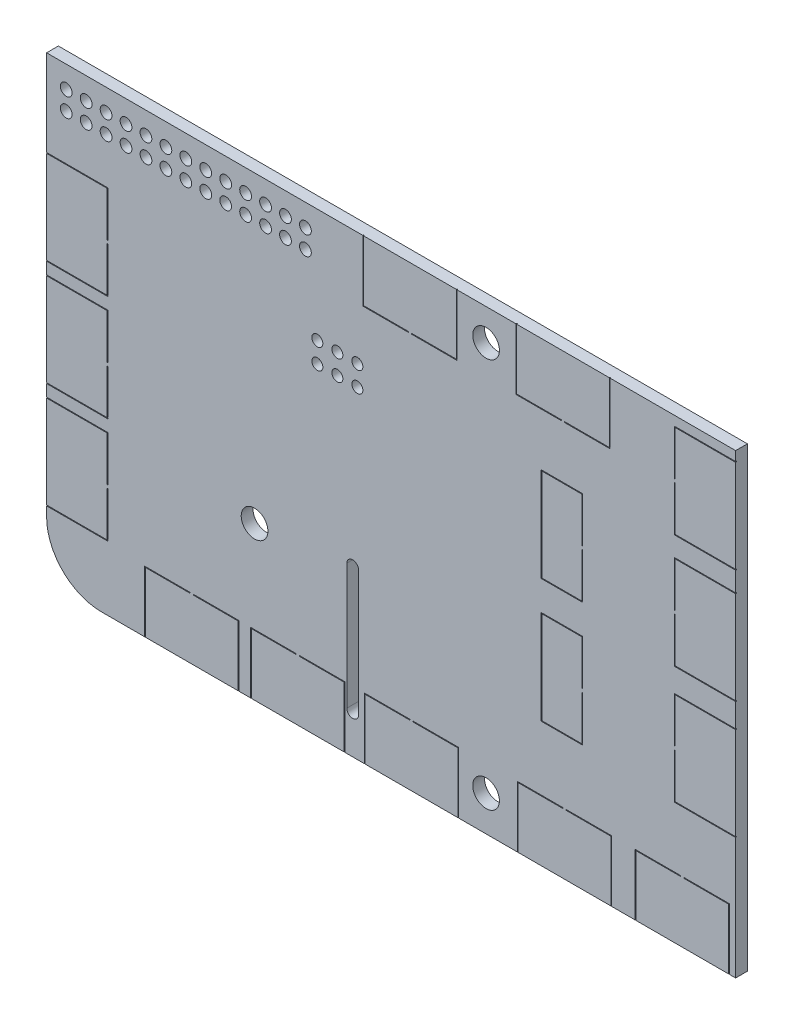
SolidWorks part; units mm, degrees
ref_plane "Plan de face" through (0, 0, 0) normal (0, 0, 1) x (1, 0, 0)
ref_plane "Plan de dessus" through (0, 0, 0) normal (0, 1, 0) x (1, 0, 0)
ref_plane "Plan de droite" through (0, 0, 0) normal (1, 0, 0) x (0, 0, -1)
sketch "Esquisse1" plane through (0, 0, 0) normal (0, 0, 1) x (1, 0, 0)
  line L0 (-4.9, -8.1) -> (-4.9, -24.1) construction
  line L1 (-36.9, -29.1) -> (43.9, -29.1)
  line L2 (-43.9, -22.1) -> (-43.9, 29.1)
  line L3 (-43.9, 29.1) -> (43.9, 29.1)
  line L4 (43.9, -29.1) -> (43.9, 29.1)
  line L5 (-43.9, -29.1) -> (43.9, 29.1) construction
  line L6 (-43.9, 29.1) -> (43.9, -29.1) construction
  line L7 (-4.15, -8.1) -> (-4.15, -24.1)
  line L8 (-5.65, -8.1) -> (-5.65, -24.1)
  circle A0 centre (12.1, 25.1) radius 1.7
  circle A1 centre (-17.4, -9.6) radius 1.7
  circle A2 centre (12.1, -24.6) radius 1.7
  arc A3 (-4.15, -8.1) -> (-5.65, -8.1) centre (-4.9, -8.1) ccw
  arc A4 (-5.65, -24.1) -> (-4.15, -24.1) centre (-4.9, -24.1) ccw
  arc A7 (-36.9, -29.1) -> (-43.9, -22.1) centre (-36.9, -22.1) cw
  point P0 (0, 0)
  point P14 (-4.9, -16.1)
  dimension "D3" = 56
  dimension "D7" = 3.4
  dimension "D8" = 3.4
  dimension "D11" = 3.4
  dimension "D20" = 7
  dimension "D1" = 87.8
  dimension "D2" = 58.2
  dimension "D4" = 4
  dimension "D5" = 26.5
  dimension "D6" = 19.5
  dimension "D9" = 56
  dimension "D10" = 4.5
  dimension "D12" = 21
  dimension "D13" = 5
  dimension "D14" = 1.5
  dimension "D15" = 39
extrude "Boss.-Extru.1" add sketch "Esquisse1" along normal blind 1.5
sketch "Esquisse2" plane through (0, 0, 0) normal (0, 0, 1) x (1, 0, 0)
  line L0 (-47.4847, 25.1) -> (2.4782, 25.1) construction
  line L1 (43.9, 29.1) -> (-43.9, 29.1) construction
  line L2 (-43.9, 29.1) -> (-43.9, -22.1) construction
  circle A0 centre (-41.4, 26.3) radius 0.75
  circle A1 centre (-41.4, 23.9) radius 0.75
  dimension "D1" = 4
  dimension "D3" = 1.5
  dimension "D2" = 2.5
  dimension "D4" = 2.8
extrude "Enlèv. mat.-Extru.3" cut sketch "Esquisse2" along normal through all
pattern_linear "Répétition linéaire1" count 13 spacing 2.54 along (1, 0, 0) of "Enlèv. mat.-Extru.3"
sketch "Esquisse3" plane through (0, 0, 1.5) normal (0, 0, 1) x (1, 0, 0)
  line L0 (43.9, 29.1) -> (-43.9, 29.1) construction
  line L1 (-13.7498, 13.3) -> (2.4782, 13.3) construction
  line L2 (-43.9, 29.1) -> (-43.9, -22.1) construction
  circle A0 centre (-9.4, 14.6) radius 0.7
  circle A1 centre (-9.4, 12) radius 0.7
  dimension "D1" = 14.5
  dimension "D3" = 1.4
  dimension "D2" = 15.8
  dimension "D4" = 34.5
extrude "Enlèv. mat.-Extru.4" cut sketch "Esquisse3" against normal blind 1.5
pattern_linear "Répétition linéaire2" count 3 spacing 2.55 along (1, 0, 0) of "Enlèv. mat.-Extru.4"
sketch "Esquisse5" plane through (0, 0, 1.5) normal (0, 0, 1) x (1, 0, 0)
  line L0 (-43.9, 29.1) -> (-43.9, -22.1) construction
  line L1 (-46, 18) -> (-36.2, 18)
  line L2 (-46, 18) -> (-46, 6.2)
  line L3 (-46, 6.2) -> (-36.2, 6.2)
  line L4 (-36.1, 18.1) -> (-36.1, 12.3)
  line L5 (-46, 18) -> (-36.2, 6.2) construction
  line L6 (-46, 6.2) -> (-36.2, 18) construction
  line L7 (-46.1, 18.1) -> (-36.1, 18.1)
  line L8 (-46.1, 18.1) -> (-46.1, 6.1)
  line L9 (-46.1, 6.1) -> (-36.1, 6.1)
  line L10 (-36.1, 12.3) -> (-36.2, 12.3)
  line L11 (-46.1, 18.1) -> (-36.1, 6.1) construction
  line L12 (-46.1, 6.1) -> (-36.1, 18.1) construction
  line L13 (43.9, 29.1) -> (-43.9, 29.1) construction
  line L14 (-36.2, 12.3) -> (-36.2, 18)
  line L15 (-36.1, 6.1) -> (-36.1, 11.9)
  line L16 (-36.1, 11.9) -> (-36.2, 11.9)
  line L17 (-36.2, 11.9) -> (-36.2, 6.2)
  line L18 (-46, 4.5) -> (-36.2, 4.5)
  line L19 (-46, 4.5) -> (-46, -7.3)
  line L20 (-46, -7.3) -> (-36.2, -7.3)
  line L21 (-36.1, 4.6) -> (-36.1, -1.2)
  line L22 (-46, 4.5) -> (-36.2, -7.3) construction
  line L23 (-46, -7.3) -> (-36.2, 4.5) construction
  line L24 (-46.1, 4.6) -> (-36.1, 4.6)
  line L25 (-46.1, 4.6) -> (-46.1, -7.4)
  line L26 (-46.1, -7.4) -> (-36.1, -7.4)
  line L27 (-36.1, -1.2) -> (-36.2, -1.2)
  line L28 (-46.1, 4.6) -> (-36.1, -7.4) construction
  line L29 (-46.1, -7.4) -> (-36.1, 4.6) construction
  line L30 (-36.2, -1.2) -> (-36.2, 4.5)
  line L31 (-36.1, -7.4) -> (-36.1, -1.6)
  line L32 (-36.1, -1.6) -> (-36.2, -1.6)
  line L33 (-36.2, -1.6) -> (-36.2, -7.3)
  line L34 (-46, -9) -> (-36.2, -9)
  line L35 (-46, -9) -> (-46, -20.8)
  line L36 (-46, -20.8) -> (-36.2, -20.8)
  line L37 (-36.1, -8.9) -> (-36.1, -14.7)
  line L38 (-46, -9) -> (-36.2, -20.8) construction
  line L39 (-46, -20.8) -> (-36.2, -9) construction
  line L40 (-46.1, -8.9) -> (-36.1, -8.9)
  line L41 (-46.1, -8.9) -> (-46.1, -20.9)
  line L42 (-46.1, -20.9) -> (-36.1, -20.9)
  line L43 (-36.1, -14.7) -> (-36.2, -14.7)
  line L44 (-46.1, -8.9) -> (-36.1, -20.9) construction
  line L45 (-46.1, -20.9) -> (-36.1, -8.9) construction
  line L46 (-36.2, -14.7) -> (-36.2, -9)
  line L47 (-36.1, -20.9) -> (-36.1, -15.1)
  line L48 (-36.1, -15.1) -> (-36.2, -15.1)
  line L49 (-36.2, -15.1) -> (-36.2, -20.8)
  line L50 (-3.4, -21.3) -> (2.4, -21.3)
  line L51 (-31.4, -21.3) -> (-25.6, -21.3)
  line L52 (-31.4, -21.3) -> (-31.4, -31.3)
  line L53 (-31.4, -31.3) -> (-19.4, -31.3)
  line L54 (-19.4, -21.3) -> (-19.4, -31.3)
  line L55 (-31.4, -21.3) -> (-19.4, -31.3) construction
  line L56 (-31.4, -31.3) -> (-19.4, -21.3) construction
  line L57 (-25.6, -21.3) -> (-25.6, -21.4)
  line L58 (-31.3, -21.4) -> (-31.3, -31.2)
  line L59 (-31.3, -31.2) -> (-19.5, -31.2)
  line L60 (-19.5, -21.4) -> (-19.5, -31.2)
  line L61 (-31.3, -21.4) -> (-19.5, -31.2) construction
  line L62 (-31.3, -31.2) -> (-19.5, -21.4) construction
  line L63 (-25.6, -21.4) -> (-31.3, -21.4)
  line L64 (-19.4, -21.3) -> (-25.2, -21.3)
  line L65 (-25.2, -21.3) -> (-25.2, -21.4)
  line L66 (-25.2, -21.4) -> (-19.5, -21.4)
  line L67 (-36.9, -29.1) -> (43.9, -29.1) construction
  line L68 (-17.9, -21.3) -> (-12.1, -21.3)
  line L69 (-17.9, -21.3) -> (-17.9, -31.3)
  line L70 (-17.9, -31.3) -> (-5.9, -31.3)
  line L71 (-5.9, -21.3) -> (-5.9, -31.3)
  line L72 (-17.9, -21.3) -> (-5.9, -31.3) construction
  line L73 (-17.9, -31.3) -> (-5.9, -21.3) construction
  line L74 (-12.1, -21.3) -> (-12.1, -21.4)
  line L75 (-17.8, -21.4) -> (-17.8, -31.2)
  line L76 (-17.8, -31.2) -> (-6, -31.2)
  line L77 (-6, -21.4) -> (-6, -31.2)
  line L78 (-17.8, -21.4) -> (-6, -31.2) construction
  line L79 (-17.8, -31.2) -> (-6, -21.4) construction
  line L80 (-12.1, -21.4) -> (-17.8, -21.4)
  line L81 (-5.9, -21.3) -> (-11.7, -21.3)
  line L82 (-11.7, -21.3) -> (-11.7, -21.4)
  line L83 (-11.7, -21.4) -> (-6, -21.4)
  line L84 (-3.4, -21.3) -> (-3.4, -31.3)
  line L85 (-3.4, -31.3) -> (8.6, -31.3)
  line L86 (8.6, -21.3) -> (8.6, -31.3)
  line L87 (-3.4, -21.3) -> (8.6, -31.3) construction
  line L88 (-3.4, -31.3) -> (8.6, -21.3) construction
  line L89 (2.4, -21.3) -> (2.4, -21.4)
  line L90 (-3.3, -21.4) -> (-3.3, -31.2)
  line L91 (-3.3, -31.2) -> (8.5, -31.2)
  line L92 (8.5, -21.4) -> (8.5, -31.2)
  line L93 (-3.3, -21.4) -> (8.5, -31.2) construction
  line L94 (-3.3, -31.2) -> (8.5, -21.4) construction
  line L95 (2.4, -21.4) -> (-3.3, -21.4)
  line L96 (8.6, -21.3) -> (2.8, -21.3)
  line L97 (2.8, -21.3) -> (2.8, -21.4)
  line L98 (2.8, -21.4) -> (8.5, -21.4)
  line L99 (16.1, -21.3) -> (21.9, -21.3)
  line L100 (16.1, -21.3) -> (16.1, -31.3)
  line L101 (16.1, -31.3) -> (28.1, -31.3)
  line L102 (28.1, -21.3) -> (28.1, -31.3)
  line L103 (16.1, -21.3) -> (28.1, -31.3) construction
  line L104 (16.1, -31.3) -> (28.1, -21.3) construction
  line L105 (21.9, -21.3) -> (21.9, -21.4)
  line L106 (16.2, -21.4) -> (16.2, -31.2)
  line L107 (16.2, -31.2) -> (28, -31.2)
  line L108 (28, -21.4) -> (28, -31.2)
  line L109 (16.2, -21.4) -> (28, -31.2) construction
  line L110 (16.2, -31.2) -> (28, -21.4) construction
  line L111 (21.9, -21.4) -> (16.2, -21.4)
  line L112 (28.1, -21.3) -> (22.3, -21.3)
  line L113 (22.3, -21.3) -> (22.3, -21.4)
  line L114 (22.3, -21.4) -> (28, -21.4)
  line L115 (31.1, -21.3) -> (36.9, -21.3)
  line L116 (31.1, -21.3) -> (31.1, -31.3)
  line L117 (31.1, -31.3) -> (43.1, -31.3)
  line L118 (43.1, -21.3) -> (43.1, -31.3)
  line L119 (31.1, -21.3) -> (43.1, -31.3) construction
  line L120 (31.1, -31.3) -> (43.1, -21.3) construction
  line L121 (36.9, -21.3) -> (36.9, -21.4)
  line L122 (31.2, -21.4) -> (31.2, -31.2)
  line L123 (31.2, -31.2) -> (43, -31.2)
  line L124 (43, -21.4) -> (43, -31.2)
  line L125 (31.2, -21.4) -> (43, -31.2) construction
  line L126 (31.2, -31.2) -> (43, -21.4) construction
  line L127 (36.9, -21.4) -> (31.2, -21.4)
  line L128 (43.1, -21.3) -> (37.3, -21.3)
  line L129 (37.3, -21.3) -> (37.3, -21.4)
  line L130 (37.3, -21.4) -> (43, -21.4)
  line L131 (36.1, -7.4) -> (36.2, -7.4)
  line L132 (36.1, -1.6) -> (46.1, -1.6)
  line L133 (36.1, -1.6) -> (36.1, -7.4)
  line L134 (36.1, -13.6) -> (46.1, -13.6)
  line L135 (46.1, -1.6) -> (46.1, -13.6)
  line L136 (36.1, -1.6) -> (46.1, -13.6) construction
  line L137 (36.1, -13.6) -> (46.1, -1.6) construction
  line L138 (36.2, -7.4) -> (36.2, -1.7)
  line L139 (36.2, -13.5) -> (46, -13.5)
  line L140 (36.1, -13.6) -> (36.1, -7.8)
  line L141 (36.2, -1.7) -> (46, -1.7)
  line L142 (46, -13.5) -> (46, -1.7)
  line L143 (36.2, -13.5) -> (46, -1.7) construction
  line L144 (36.2, -1.7) -> (46, -13.5) construction
  line L145 (36.1, -7.8) -> (36.2, -7.8)
  line L146 (36.2, -7.8) -> (36.2, -13.5)
  line L147 (43.9, -29.1) -> (43.9, 29.1) construction
  line L148 (36.1, 7.6) -> (36.2, 7.6)
  line L149 (36.1, 13.4) -> (46.1, 13.4)
  line L150 (36.1, 13.4) -> (36.1, 7.6)
  line L151 (36.1, 1.4) -> (46.1, 1.4)
  line L152 (46.1, 13.4) -> (46.1, 1.4)
  line L153 (36.1, 13.4) -> (46.1, 1.4) construction
  line L154 (36.1, 1.4) -> (46.1, 13.4) construction
  line L155 (36.2, 7.6) -> (36.2, 13.3)
  line L156 (36.2, 1.5) -> (46, 1.5)
  line L157 (36.1, 1.4) -> (36.1, 7.2)
  line L158 (36.2, 13.3) -> (46, 13.3)
  line L159 (46, 1.5) -> (46, 13.3)
  line L160 (36.2, 1.5) -> (46, 13.3) construction
  line L161 (36.2, 13.3) -> (46, 1.5) construction
  line L162 (36.1, 7.2) -> (36.2, 7.2)
  line L163 (36.2, 7.2) -> (36.2, 1.5)
  line L164 (36.1, 22.1) -> (36.2, 22.1)
  line L165 (36.1, 27.9) -> (46.1, 27.9)
  line L166 (36.1, 27.9) -> (36.1, 22.1)
  line L167 (36.1, 15.9) -> (46.1, 15.9)
  line L168 (46.1, 27.9) -> (46.1, 15.9)
  line L169 (36.1, 27.9) -> (46.1, 15.9) construction
  line L170 (36.1, 15.9) -> (46.1, 27.9) construction
  line L171 (36.2, 22.1) -> (36.2, 27.8)
  line L172 (36.2, 16) -> (46, 16)
  line L173 (36.1, 15.9) -> (36.1, 21.7)
  line L174 (36.2, 27.8) -> (46, 27.8)
  line L175 (46, 16) -> (46, 27.8)
  line L176 (36.2, 16) -> (46, 27.8) construction
  line L177 (36.2, 27.8) -> (46, 16) construction
  line L178 (36.1, 21.7) -> (36.2, 21.7)
  line L179 (36.2, 21.7) -> (36.2, 16)
  line L180 (15.9, 21.3) -> (21.7, 21.3)
  line L181 (15.9, 31.3) -> (27.9, 31.3)
  line L182 (15.9, 31.3) -> (15.9, 21.3)
  line L183 (21.7, 21.3) -> (21.7, 21.4)
  line L184 (27.9, 31.3) -> (27.9, 21.3)
  line L185 (15.9, 31.3) -> (27.9, 21.3) construction
  line L186 (15.9, 21.3) -> (27.9, 31.3) construction
  line L187 (21.7, 21.4) -> (16, 21.4)
  line L188 (16, 21.4) -> (16, 31.2)
  line L189 (16, 31.2) -> (27.8, 31.2)
  line L190 (27.8, 21.4) -> (27.8, 31.2)
  line L191 (16, 21.4) -> (27.8, 31.2) construction
  line L192 (16, 31.2) -> (27.8, 21.4) construction
  line L193 (27.9, 21.3) -> (22.1, 21.3)
  line L194 (22.1, 21.3) -> (22.1, 21.4)
  line L195 (22.1, 21.4) -> (27.8, 21.4)
  line L196 (-3.6, 21.3) -> (2.2, 21.3)
  line L197 (-3.6, 31.3) -> (8.4, 31.3)
  line L198 (-3.6, 31.3) -> (-3.6, 21.3)
  line L199 (2.2, 21.3) -> (2.2, 21.4)
  line L200 (8.4, 31.3) -> (8.4, 21.3)
  line L201 (-3.6, 31.3) -> (8.4, 21.3) construction
  line L202 (-3.6, 21.3) -> (8.4, 31.3) construction
  line L203 (2.2, 21.4) -> (-3.5, 21.4)
  line L204 (-3.5, 21.4) -> (-3.5, 31.2)
  line L205 (-3.5, 31.2) -> (8.3, 31.2)
  line L206 (8.3, 21.4) -> (8.3, 31.2)
  line L207 (-3.5, 21.4) -> (8.3, 31.2) construction
  line L208 (-3.5, 31.2) -> (8.3, 21.4) construction
  line L209 (8.4, 21.3) -> (2.6, 21.3)
  line L210 (2.6, 21.3) -> (2.6, 21.4)
  line L211 (2.6, 21.4) -> (8.3, 21.4)
  line L212 (24.4, 14.6) -> (24.4, 8.8)
  line L213 (19.1, 14.6) -> (24.4, 14.6)
  line L214 (19.1, 14.6) -> (19.1, 2.6)
  line L215 (19.1, 2.6) -> (24.4, 2.6)
  line L216 (24.4, 8.8) -> (24.3, 8.8)
  line L217 (19.1, 14.6) -> (24.4, 2.6) construction
  line L218 (19.1, 2.6) -> (24.4, 14.6) construction
  line L219 (19.2, 2.7) -> (24.3, 2.7)
  line L220 (19.2, 2.7) -> (19.2, 14.5)
  line L221 (19.2, 14.5) -> (24.3, 14.5)
  line L222 (24.3, 8.8) -> (24.3, 14.5)
  line L223 (19.2, 2.7) -> (24.3, 14.5) construction
  line L224 (19.2, 14.5) -> (24.3, 2.7) construction
  line L225 (24.4, 2.6) -> (24.4, 8.4)
  line L226 (24.4, 8.4) -> (24.3, 8.4)
  line L227 (24.3, 8.4) -> (24.3, 2.7)
  line L228 (24.4, -1.15) -> (24.4, -6.95)
  line L229 (19.1, -1.15) -> (24.4, -1.15)
  line L230 (19.1, -1.15) -> (19.1, -13.15)
  line L231 (19.1, -13.15) -> (24.4, -13.15)
  line L232 (24.4, -6.95) -> (24.3, -6.95)
  line L233 (19.1, -1.15) -> (24.4, -13.15) construction
  line L234 (19.1, -13.15) -> (24.4, -1.15) construction
  line L235 (19.2, -13.05) -> (24.3, -13.05)
  line L236 (19.2, -13.05) -> (19.2, -1.25)
  line L237 (19.2, -1.25) -> (24.3, -1.25)
  line L238 (24.3, -6.95) -> (24.3, -1.25)
  line L239 (19.2, -13.05) -> (24.3, -1.25) construction
  line L240 (19.2, -1.25) -> (24.3, -13.05) construction
  line L241 (24.4, -13.15) -> (24.4, -7.35)
  line L242 (24.4, -7.35) -> (24.3, -7.35)
  line L243 (24.3, -7.35) -> (24.3, -13.05)
  point P0 (-41.1, 12.1)
  point P5 (-41.1, 12.1)
  point P18 (-41.1, -1.4)
  point P23 (-41.1, -1.4)
  point P32 (-41.1, -14.9)
  point P37 (-41.1, -14.9)
  point P46 (-25.4, -26.3)
  point P51 (-25.4, -26.3)
  point P62 (-11.9, -26.3)
  point P67 (-11.9, -26.3)
  point P76 (2.6, -26.3)
  point P81 (2.6, -26.3)
  point P90 (22.1, -26.3)
  point P95 (22.1, -26.3)
  point P104 (37.1, -26.3)
  point P109 (37.1, -26.3)
  point P118 (41.1, -7.6)
  point P125 (41.1, -7.6)
  point P134 (41.1, 7.4)
  point P140 (41.1, 7.4)
  point P148 (41.1, 21.9)
  point P154 (41.1, 21.9)
  point P162 (21.9, 26.3)
  point P167 (21.9, 26.3)
  point P172 (2.4, 26.3)
  point P181 (2.4, 26.3)
  point P190 (21.75, 8.6)
  point P195 (21.75, 8.6)
  point P200 (21.75, -7.15)
  point P209 (21.75, -7.15)
  dimension "D1" = 5.8
  dimension "D2" = 12
  dimension "D3" = 0.1
  dimension "D4" = 5.8
  dimension "D5" = 11
  dimension "D6" = 10
  dimension "D7" = 0.1
  dimension "D8" = 0.1
  dimension "D9" = 7.8
  dimension "D10" = 12
  dimension "D11" = 0.1
  dimension "D12" = 5.8
  dimension "D13" = 5.8
  dimension "D14" = 10
  dimension "D15" = 0.1
  dimension "D16" = 0.1
  dimension "D17" = 1.5
  dimension "D18" = 7.8
  dimension "D19" = 12
  dimension "D20" = 5.8
  dimension "D21" = 5.8
  dimension "D22" = 10
  dimension "D23" = 0.1
  dimension "D24" = 0.1
  dimension "D25" = 1.5
  dimension "D26" = 7.8
  dimension "D27" = 0.1
  dimension "D28" = 12
  dimension "D29" = 0.1
  dimension "D30" = 0.1
  dimension "D31" = 12.5
  dimension "D32" = 5.8
  dimension "D33" = 5.8
  dimension "D34" = 7.8
  dimension "D35" = 0.1
  dimension "D36" = 10
  dimension "D37" = 0.1
  dimension "D38" = 5.8
  dimension "D39" = 5.8
  dimension "D40" = 0.1
  dimension "D41" = 10
  dimension "D42" = 1.5
  dimension "D43" = 7.8
  dimension "D44" = 0.1
  dimension "D45" = 12
  dimension "D46" = 0.1
  dimension "D47" = 5.8
  dimension "D48" = 5.8
  dimension "D49" = 0.1
  dimension "D50" = 10
  dimension "D51" = 0.1
  dimension "D52" = 12
  dimension "D53" = 2.5
  dimension "D54" = 7.8
  dimension "D55" = 0.1
  dimension "D56" = 5.8
  dimension "D57" = 5.8
  dimension "D58" = 0.1
  dimension "D59" = 10
  dimension "D60" = 0.1
  dimension "D61" = 12
  dimension "D62" = 7.8
  dimension "D63" = 7.5
  dimension "D64" = 0.1
  dimension "D65" = 5.8
  dimension "D66" = 5.8
  dimension "D67" = 0.1
  dimension "D68" = 10
  dimension "D69" = 0.1
  dimension "D70" = 12
  dimension "D71" = 7.8
  dimension "D72" = 3
  dimension "D73" = 12
  dimension "D74" = 7.8
  dimension "D75" = 10
  dimension "D76" = 15.5
  dimension "D77" = 0.1
  dimension "D78" = 0.1
  dimension "D79" = 5.8
  dimension "D80" = 0.1
  dimension "D81" = 5.8
  dimension "D82" = 12
  dimension "D83" = 0.1
  dimension "D84" = 0.1
  dimension "D85" = 10
  dimension "D86" = 5.8
  dimension "D87" = 0.1
  dimension "D88" = 5.8
  dimension "D89" = 7.8
  dimension "D90" = 3
  dimension "D91" = 12
  dimension "D92" = 0.1
  dimension "D93" = 10
  dimension "D94" = 5.8
  dimension "D95" = 0.1
  dimension "D96" = 5.8
  dimension "D97" = 7.8
  dimension "D98" = 0.1
  dimension "D99" = 2.5
  dimension "D100" = 12
  dimension "D101" = 10
  dimension "D102" = 5.8
  dimension "D103" = 16
  dimension "D104" = 0.1
  dimension "D105" = 0.1
  dimension "D106" = 5.8
  dimension "D107" = 0.1
  dimension "D108" = 7.8
  dimension "D109" = 12
  dimension "D110" = 10
  dimension "D111" = 0.1
  dimension "D112" = 0.1
  dimension "D113" = 5.8
  dimension "D114" = 5.8
  dimension "D115" = 0.1
  dimension "D116" = 7.8
  dimension "D117" = 7.5
  dimension "D118" = 5.3
  dimension "D119" = 12
  dimension "D120" = 19.5
  dimension "D121" = 14.5
  dimension "D122" = 0.1
  dimension "D123" = 0.1
  dimension "D124" = 5.8
  dimension "D125" = 5.8
  dimension "D126" = 0.1
  dimension "D127" = 0.1
  dimension "D128" = 5.3
  dimension "D129" = 12
  dimension "D130" = 0.1
  dimension "D131" = 0.1
  dimension "D132" = 5.8
  dimension "D133" = 5.8
  dimension "D134" = 0.1
  dimension "D135" = 0.1
  dimension "D136" = 3.75
  dimension "D137" = 19.5
extrude "Enlèv. mat.-Extru.8" cut sketch "Esquisse5" against normal blind 0.1
